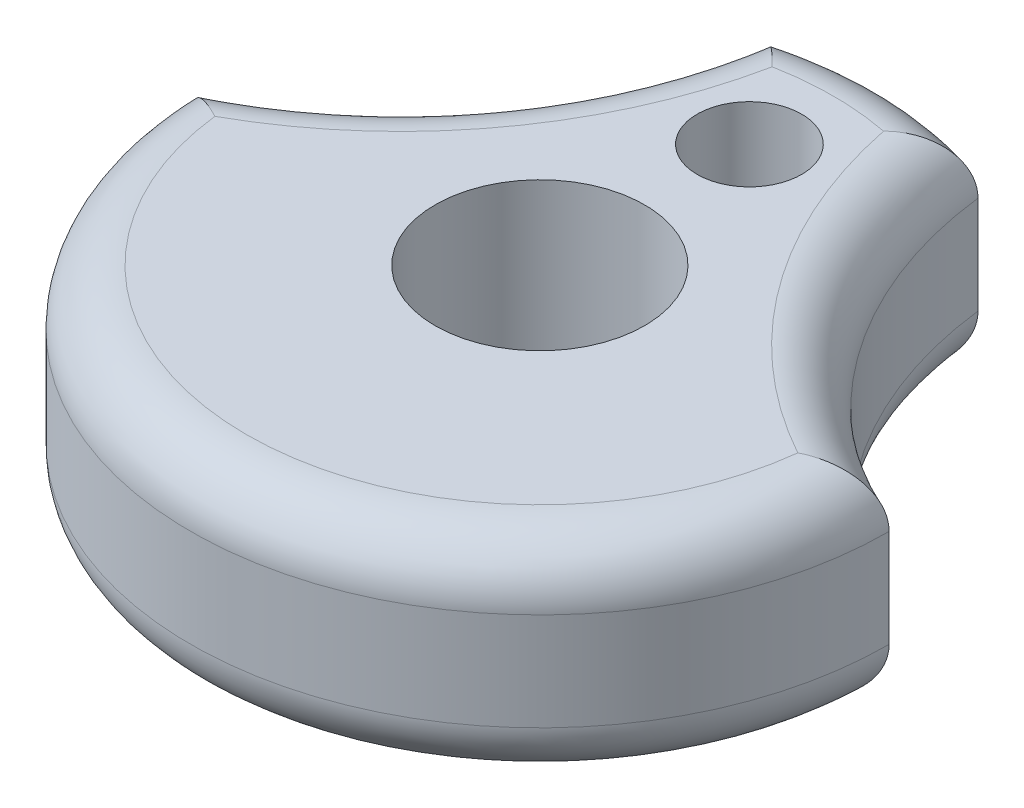
SolidWorks part; units mm, degrees
material "Plain Carbon Steel"
ref_plane "Front Plane" through (0, 0, 0) normal (0, 0, 1) x (1, 0, 0)
ref_plane "Top Plane" through (0, 0, 0) normal (0, 1, 0) x (1, 0, 0)
ref_plane "Right Plane" through (0, 0, 0) normal (1, 0, 0) x (0, 0, -1)
sketch "Sketch1" plane through (0, 0, 0) normal (0, 1, 0) x (1, 0, 0)
  line L0 (0, 0) -> (50000, 0) construction
  line L1 (0, 0) -> (0, 50000) construction
  line L2 (4.7752, 21.5226) -> (4.7752, 50021.5226) construction
  line L3 (-4.7752, 21.5226) -> (-4.7752, 50021.5226) construction
  arc A0 (-15.875, 0) -> (15.875, 0) centre (0, 0) ccw
  circle A1 centre (0, 0) radius 4.7625
  circle A2 centre (0, 9.525) radius 2.3749
  arc A3 (4.7752, 15.1398) -> (15.875, 0) centre (23.694, 17.3714) ccw
  arc A4 (-4.7752, 15.1398) -> (-15.875, 0) centre (-23.694, 17.3714) cw
  arc A5 (4.7752, 15.1398) -> (-4.7752, 15.1398) centre (0, 0) ccw
  dimension "D1" = 31.75
  dimension "D2" = 9.525
  dimension "D5" = 4.7498
  dimension "D6" = 19.05
  dimension "D3" = 4.7752
  dimension "D4" = 9.525
extrude "Boss-Extrude1" add sketch "Sketch1" along normal mid plane 9.525
fillet "Fillet1" radius 2.54 8 edges at (0, -4.7625, -15.875) (-8.3307, -4.7625, -6.1077) (8.3307, -4.7625, -6.1077) (0, -4.7625, 15.875) (8.3307, 4.7625, -6.1077) (0, 4.7625, -15.875) (0, 4.7625, 15.875) (-8.3307, 4.7625, -6.1077)
